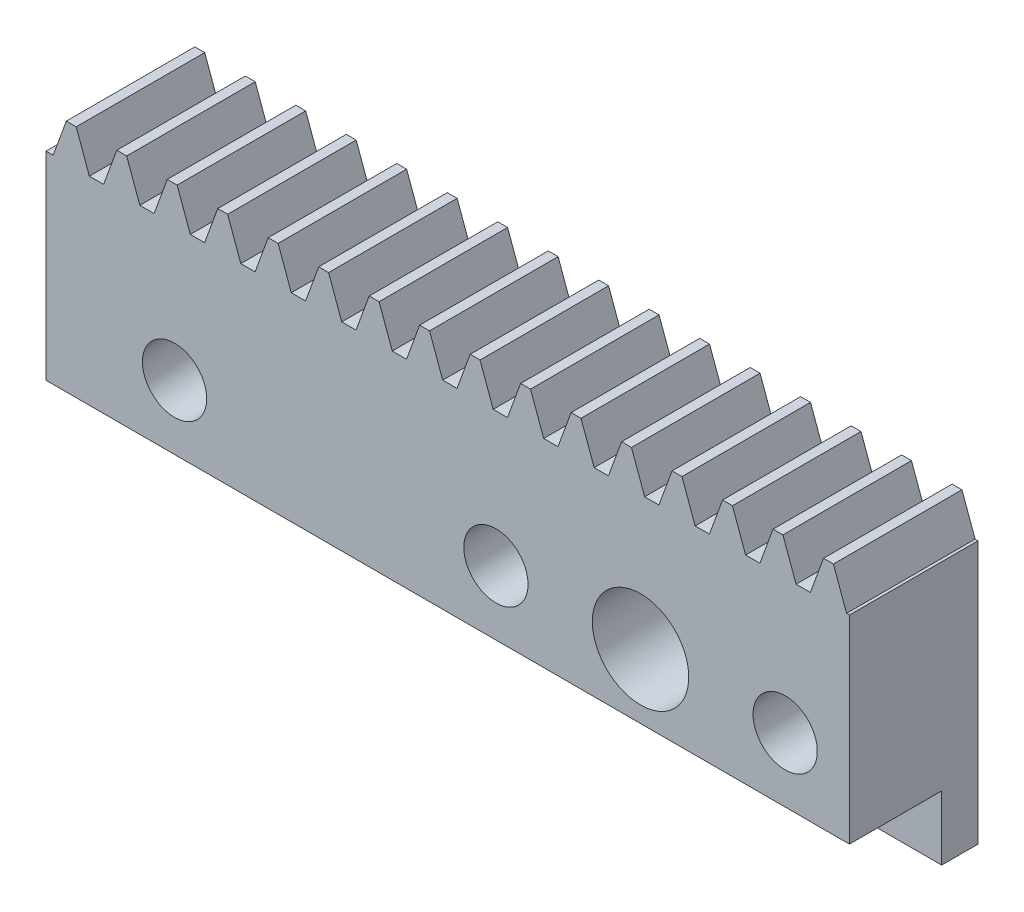
SolidWorks part; units mm, degrees
extrude "Blank" add sketch "BlankSke" against normal blind 4
sketch "BlankSke" plane through (0, 0, 0) normal (0, 0, 1) x (1, 0, 0)
  line L1 (0, 0) -> (25, 0)
  line L2 (0, 0) -> (0, 7.3)
  line L3 (0, 7.3) -> (25, 7.3)
  line L4 (25, 0) -> (25, 7.3)
  dimension "Length" = 25
  dimension "Blank_height" = 7.3
ref_plane "Plane1" through (0, 0, 0) normal (0, 0, 1) x (1, 0, 0)
ref_plane "Plane2" through (0, 0, 0) normal (0, 1, 0) x (1, 0, 0)
ref_plane "Plane3" through (0, 0, 0) normal (1, 0, 0) x (0, 0, -1)
sketch "HoldingSke" plane through (0, 0, 0) normal (0, 1, 0) x (1, 0, 0)
  line L0 (0, 0) -> (0.2783, 1.9805)
  line L1 (-15, 0) -> (100, 0) construction
  line L2 (0, 0) -> (-2.1039, 2.3779)
  line L3 (0, 0) -> (-11.863, 4.5341)
  line L4 (0, 0) -> (8.2587, 2.5249)
  line L5 (0, 0) -> (-23.7986, -8.8762)
  line L6 (0, 0) -> (-10.5278, -7.1032)
  line L9 (-71.009, 38.7566) -> (-47.5167, 47.3071)
  line L10 (-76.2, 2.8779) -> (-69.4, 2.8779)
  line L11 (0, 0) -> (-4, 0)
  line L12 (-76.2, 101.6) -> (-76.181, 101.6)
  line L13 (24.9733, 27.94) -> (52.9518, 28.4284)
  line L14 (24.9733, 27.94) -> (24.9743, 27.94)
  line L15 (24.9733, 27.94) -> (100.4006, 29.5858)
  circle A0 centre (0, 0) radius 19.05
  circle A1 centre (0, 0) radius 3.4
  circle A2 centre (0, 0) radius 12.7
  dimension "MPH" = 6.8
  dimension "Diameter" = 38.1
  dimension "Num_teeth" = 17
  dimension "Pitch" = 2
  dimension "Show_teeth" = 998
  dimension "Thickness" = 12.7
  dimension "Ap" = 20
  dimension "Pitch_height" = 6.8
  dimension "Width" = 4
  dimension "Backlash" = 0.019
  dimension "Addendum_fac" = 1
  dimension "Dedendum_fac" = 1.25
  dimension "Clearance_fac" = 0.25
  dimension "Dedendum_add" = 0.001
  dimension "Length" = 25
  dimension "Module" = 0.5
sketch "TooCutSkeIll" plane through (0, 0, 0) normal (0, 0, 1) x (1, 0, 0)
  line L0 (-0.6269, 7.2868) -> (-0.2524, 6.2579)
  line L1 (-0.134, 6.175) -> (0.134, 6.175)
  line L2 (0.2524, 6.2579) -> (0.6269, 7.2868)
  line L3 (25, 7.3) -> (0, 7.3) construction
  line L4 (0, 0) -> (0, 64.897) construction
  line L5 (-13.208, 6.8) -> (12.954, 6.8) construction
  line L6 (0, 0) -> (25, 0) construction
  line L7 (0.4497, 6.8) -> (0.4497, 48.7463) construction
  line L8 (-0.4497, 6.8) -> (-0.4497, 48.7463) construction
  line L9 (0.6457, 7.3) -> (0.6457, 7.3254)
  line L10 (-0.6457, 7.3) -> (-0.6457, 7.3254)
  line L11 (-0.6457, 7.3254) -> (0.6457, 7.3254)
  arc A0 (0.134, 6.175) -> (0.2524, 6.2579) centre (0.134, 6.301) ccw
  arc A1 (-0.2524, 6.2579) -> (-0.134, 6.175) centre (-0.134, 6.301) ccw
  arc A2 (0.6457, 7.3) -> (0.6269, 7.2868) centre (0.6457, 7.28) ccw
  arc A3 (-0.6269, 7.2868) -> (-0.6457, 7.3) centre (-0.6457, 7.28) ccw
  dimension "Pitch_height" = 6.8
  dimension "Addendum_plus" = 0.5254
  dimension "Pressure_angle" = 20
  dimension "Gap_width" = 0.8994
  dimension "Dedendum" = 0.625
extrude "ToothCutIll" [suppressed] cut sketch "TooCutSkeIll" against normal through all
sketch "TooCutSkeSim" plane through (0, 0, 0) normal (0, 0, 1) x (1, 0, 0)
  line L0 (0.2222, 6.175) -> (-0.2222, 6.175)
  line L1 (0.6409, 7.3254) -> (0.2222, 6.175)
  line L2 (0, 17.4625) -> (0, 53.467) construction
  line L3 (0.6409, 7.3254) -> (-0.6409, 7.3254)
  line L6 (-0.6409, 7.3254) -> (-0.2222, 6.175)
  line L9 (-0.4497, 6.8) -> (0.4497, 6.8) construction
  line L10 (0, 0) -> (25, 0) construction
  line L11 (0.4497, 6.8) -> (0.4497, 53.467) construction
  line L12 (-0.4497, 6.8) -> (-0.4497, 53.467) construction
  dimension "Pitch_height" = 6.8
  dimension "Addendum_plus" = 0.5254
  dimension "Pressure_angle" = 20
  dimension "Gap_width" = 0.8994
  dimension "Dedendum" = 0.625
extrude "ToothCutSim" cut sketch "TooCutSkeSim" against normal through all
pattern_linear "TeethCuts" count 17 spacing 1.5708 along (1, 0, 0) of "ToothCutIll", "ToothCutSim"
sketch "Sketch1" plane through (0, 0, -4) normal (0, 0, -1) x (-1, 0, 0)
  line L0 (-23, 2) -> (-25, 2)
  line L2 (-25, 0) -> (-25, 6.175) construction
  line L3 (-23, 0) -> (-23, 1)
  line L4 (0, 0) -> (-25, 0) construction
  line L5 (-23, 1) -> (-23, 3)
  line L6 (-22, 2) -> (-20, 2)
  line L7 (-20, 2) -> (-17, 2)
  line L8 (-17, 2) -> (-15, 2)
  line L9 (-15, 2) -> (-13, 2)
  line L10 (-13, 2) -> (-5, 2)
  line L11 (-5, 2) -> (-3, 2)
  circle A1 centre (-23, 2) radius 1
  circle A2 centre (-18.5, 2) radius 1.5
  circle A3 centre (-14, 2) radius 1
  circle A4 centre (-4, 2) radius 1
extrude "Cut-Extrude1" cut sketch "Sketch1" against normal through all contours L0 A1 L5 | A1 L5 | L5 A1 L0 | L7 A2 | L7 A2 | L9 A3 | L9 A3 | L11 A4 | L11 A4
sketch "Sketch4" plane through (0, 0, 0) normal (0, -1, 0) x (1, 0, 0)
  line L0 (0, -50) -> (0, 50) construction
  line L1 (0, -4) -> (25, -4)
  line L2 (0, -4) -> (0, -2.87)
  line L3 (0, -2.87) -> (25, -2.87)
  line L4 (25, -4) -> (25, -2.87)
  line L5 (0, -4) -> (25, -4) construction
  line L6 (25, -4) -> (25, 0) construction
  dimension "D1" = 1.13
extrude "Boss-Extrude1" add sketch "Sketch4" along normal blind 2
equation "' \"Module@HoldingSke\" = 6.35"
equation "' \"Num_teeth@HoldingSke\" = 12"
equation "' \"Ap@HoldingSke\" =  20"
equation "' \"Ap@HoldingSke\" = 20"
equation "' \"Width@HoldingSke\" = 0.25 * 25.4"
equation "' \"Show_teeth@HoldingSke\" = 500"
equation "' \"Backlash@HoldingSke\" = 0.009 * 25.4"
equation "' \"Addendum_fac@HoldingSke\" = 1.0"
equation "' \"Dedendum_fac@HoldingSke\" = 1.25"
equation "' \"Dedendum_add@HoldingSke\" = 0.00005 * 25.4"
equation "' \"Clearance_fac@HoldingSke\" = 0.25"
equation "' \"Pitch_height@HoldingSke\" = 1 * 25.4"
equation "' \"Length@HoldingSke\" = 4.71 * 25.4"
equation "\"Pitch@HoldingSke\" = 1 / \"Module@HoldingSke\""
equation "\"MPH@HoldingSke\" = \"Dedendum_fac@HoldingSke\" / \"Pitch@HoldingSke\" + 2 * \"Dedendum_add@HoldingSke\" + 0.002 * 25.4"
equation "\"MPH@HoldingSke\" = ((sgn( \"MPH@HoldingSke\" - \"Pitch_height@HoldingSke\")+1)*( \"MPH@HoldingSke\" - \"Pitch_height@HoldingSke\"))/2 + \"Pitch_height@HoldingSke\""
equation "\"Blank_height@BlankSke\" = \"Pitch_height@HoldingSke\" + \"Addendum_fac@HoldingSke\"  / \"Pitch@HoldingSke\" "
equation "\"Length@BlankSke\" =  \"Length@HoldingSke\""
equation "\"Face_width@Blank\" = \"Width@HoldingSke\""
equation "\"Pressure_angle@TooCutSkeIll\" = \"Ap@HoldingSke\""
equation "\"Addendum_plus@TooCutSkeIll\" =  \"Addendum_fac@HoldingSke\"  / \"Pitch@HoldingSke\" + 0.001 *25.4"
equation "\"Dedendum@TooCutSkeIll\" = \"Dedendum_fac@HoldingSke\"  / \"Pitch@HoldingSke\""
equation "\"Pitch_height@TooCutSkeIll\" =  \"MPH@HoldingSke\""
equation "\"Gap_width@TooCutSkeIll\" = 3.14159265 / 2 / \"Pitch@HoldingSke\" + 6 * \"Backlash@HoldingSke\""
equation "\"Pressure_angle@TooCutSkeSim\" = \"Ap@HoldingSke\""
equation "\"Addendum_plus@TooCutSkeSim\" =  \"Addendum_fac@HoldingSke\"  / \"Pitch@HoldingSke\" + 0.001 * 25.4"
equation "\"Dedendum@TooCutSkeSim\" = \"Dedendum_fac@HoldingSke\"  / \"Pitch@HoldingSke\""
equation "\"Pitch_height@TooCutSkeSim\" =  \"MPH@HoldingSke\""
equation "\"Gap_width@TooCutSkeSim\" = 3.14159265 / 2 / \"Pitch@HoldingSke\" + 6 * \"Backlash@HoldingSke\""
equation "\"Root_fillet@TooCutSkeIll\" = \"Clearance_fac@HoldingSke\" / \"Pitch@HoldingSke\" + \"Dedendum_add@HoldingSke\""
equation "\"Break_rad@TooCutSkeIll\" = 0.02 / \"Pitch@HoldingSke\" * 2"
equation "\"Linear_pitch@TeethCuts\" = 3.14159265 / \"Pitch@HoldingSke\""
equation "\"Num_teeth@HoldingSke\" = int( ( \"Length@HoldingSke\" + 0 ) / (3.14159265 / \"Pitch@HoldingSke\")) + 0.9999  + 1"
equation " \"Num_teeth@TeethCuts\" = int( \"Show_teeth@HoldingSke\" ) + 1"
equation " \"Num_teeth@TeethCuts\" = ((sgn( \"Num_teeth@TeethCuts\" - \"Num_teeth@HoldingSke\" )-1)*( \"Num_teeth@TeethCuts\" - \"Num_teeth@HoldingSke\" ))/-2+ \"Num_teeth@HoldingSke\""
equation " \"Num_teeth@TeethCuts\" = ((sgn( \"Num_teeth@TeethCuts\" - 2.0)+1)*( \"Num_teeth@TeethCuts\" - 2.0))/2 +2.0"
